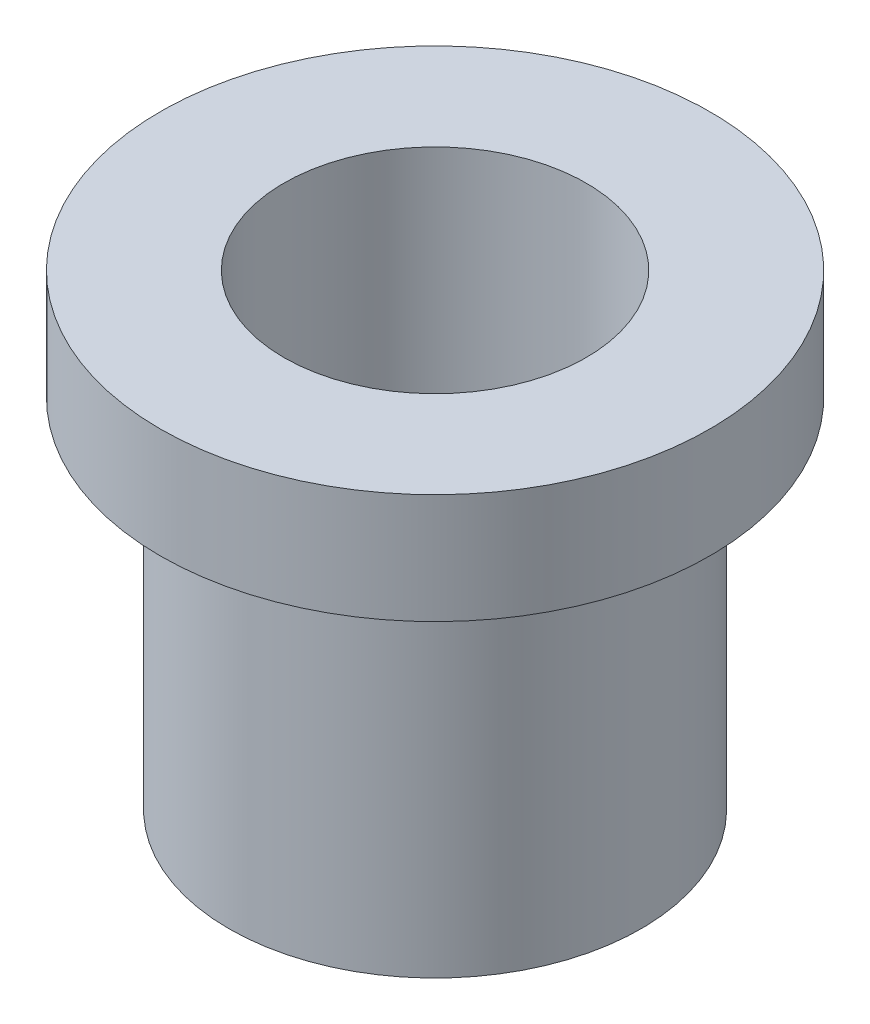
SolidWorks part; units mm, degrees
material "PLA - 20% infill"
ref_plane "Front Plane" through (0, 0, 0) normal (0, 0, 1) x (1, 0, 0)
ref_plane "Top Plane" through (0, 0, 0) normal (0, 1, 0) x (1, 0, 0)
ref_plane "Right Plane" through (0, 0, 0) normal (1, 0, 0) x (0, 0, -1)
sketch "Sketch2" plane through (0, 0, 0) normal (0, 1, 0) x (1, 0, 0)
  circle A0 centre (0, 0) radius 3.75
  dimension "D1" = 7.5
extrude "Boss-Extrude1" add sketch "Sketch2" along normal blind 6.5
sketch "Sketch3" plane through (0, 6.5, 0) normal (0, 1, 0) x (1, 0, 0)
  circle A0 centre (0, 0) radius 5
  dimension "D1" = 10
extrude "Boss-Extrude2" add sketch "Sketch3" along normal blind 2
sketch "Sketch4" plane through (0, 0, 0) normal (0, -1, 0) x (1, 0, 0)
  circle A0 centre (0, 0) radius 1.25
  dimension "D1" = 2.5
extrude "Cut-Extrude1" cut sketch "Sketch4" against normal offset from surface (6.5 mm away) 2 up to face at (0, 8.5, 5)
sketch "Sketch5" plane through (0, 8.5, 0) normal (0, 1, 0) x (1, 0, 0)
  circle A0 centre (0, 0) radius 2.75
  dimension "D1" = 5.5
extrude "Cut-Extrude2" cut sketch "Sketch5" against normal blind 5
